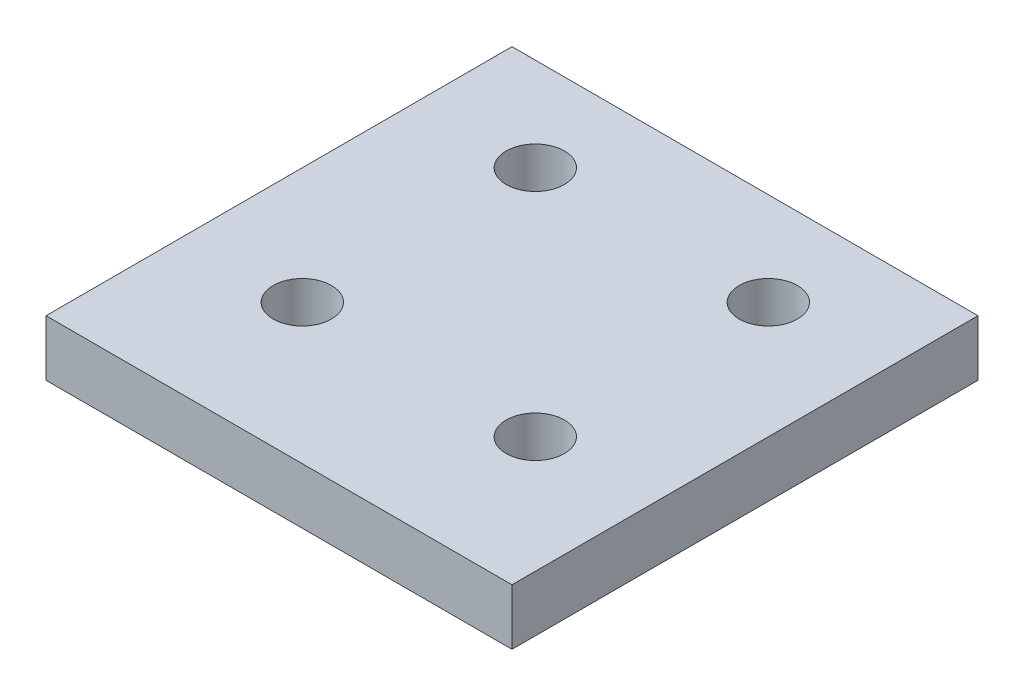
SolidWorks part; units mm, degrees
ref_plane "Front Plane" through (0, 0, 0) normal (0, 0, 1) x (1, 0, 0)
ref_plane "Top Plane" through (0, 0, 0) normal (0, 1, 0) x (1, 0, 0)
ref_plane "Right Plane" through (0, 0, 0) normal (1, 0, 0) x (0, 0, -1)
sketch "Sketch1" plane through (0, 0, 0) normal (0, 1, 0) x (1, 0, 0)
  line L1 (0, 0) -> (-50.8, 0)
  line L2 (0, 0) -> (0, 50.8)
  line L3 (0, 50.8) -> (-50.8, 50.8)
  line L4 (-50.8, 0) -> (-50.8, 50.8)
  circle A0 centre (-38.1, 40.64) radius 3.175
  circle A1 centre (-12.7, 40.64) radius 3.175
  circle A2 centre (-12.7, 15.24) radius 3.175
  circle A3 centre (-38.1, 15.24) radius 3.175
  dimension "D3" = 6.35
  dimension "D4" = 6.35
  dimension "D5" = 6.35
  dimension "D6" = 6.35
  dimension "D7" = 12.7
  dimension "D8" = 25.4
  dimension "D9" = 12.7
  dimension "D10" = 25.4
  dimension "D11" = 10.16
  dimension "D13" = 25.4
  dimension "D14" = 25.4
  dimension "D1" = 50.8
  dimension "D2" = 50.8
  dimension "D12" = 10.16
extrude "Boss-Extrude1" add sketch "Sketch1" along normal blind 6.096
